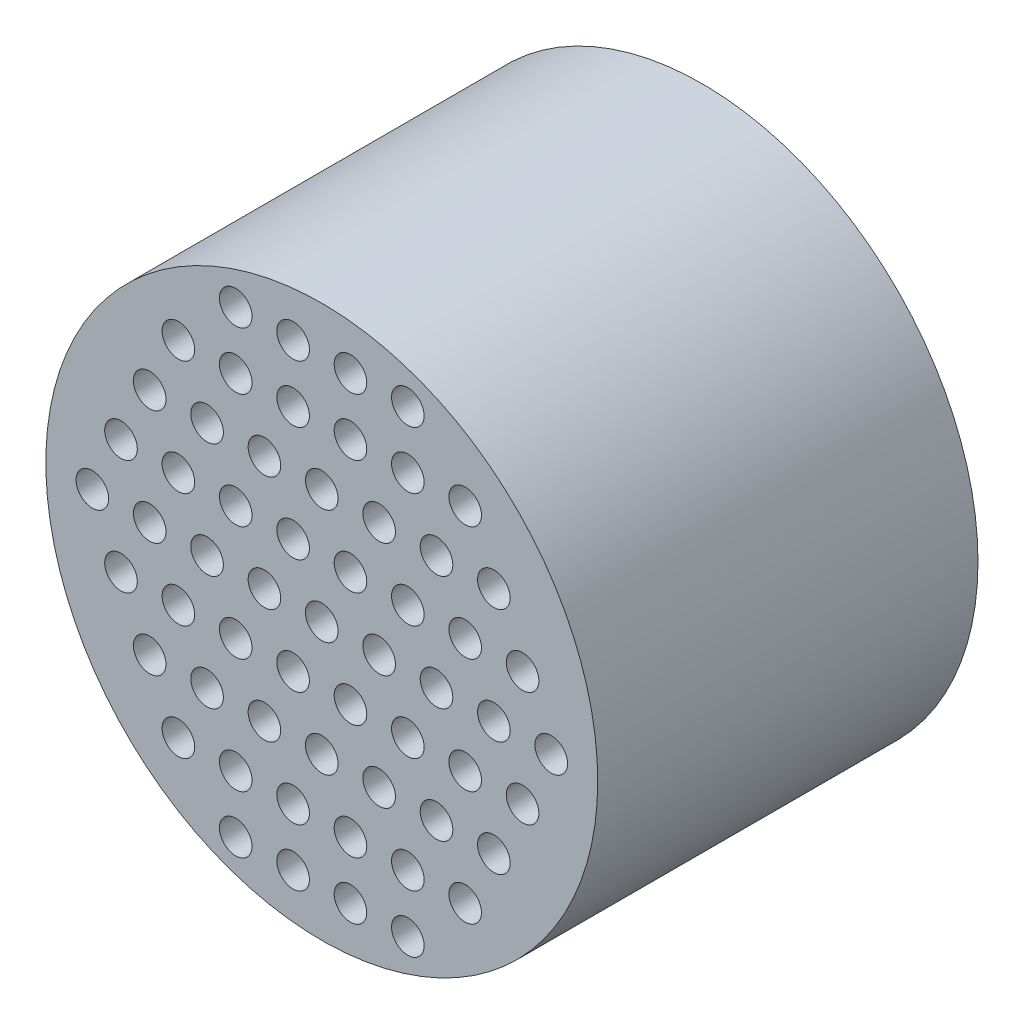
SolidWorks part; units mm, degrees
material "PBT à usage général"
ref_plane "Plan de face" through (0, 0, 0) normal (0, 0, 1) x (1, 0, 0)
ref_plane "Plan de dessus" through (0, 0, 0) normal (0, 1, 0) x (1, 0, 0)
ref_plane "Plan de droite" through (0, 0, 0) normal (1, 0, 0) x (0, 0, -1)
sketch "Esquisse1" plane through (0, 0, 0) normal (0, 0, 1) x (1, 0, 0)
  circle A0 centre (16.6252, 7.1087) radius 25.4
  dimension "D1" = 50.8
extrude "Boss.-Extru.1" add sketch "Esquisse1" along normal blind 25
sketch "Esquisse6" plane through (0, 0, 0) normal (0, 0, -1) x (-1, 0, 0)
  line L0 (-42.0252, 7.1087) -> (8.7748, 7.1087) construction
  circle A0 centre (-16.6252, 7.1087) radius 25.4 construction
  circle A1 centre (-39.5252, 7.1087) radius 1.55
  circle A2 centre (6.2748, 7.1087) radius 1.55
  point P12 (-16.6252, 7.1087)
  dimension "D1" = 3.1
  dimension "D2" = 2.5
  dimension "D3" = 2
extrude "Enlèv. mat.-Extru.4" cut sketch "Esquisse6" against normal blind 6
sketch "Esquisse8" plane through (0, 0, 25) normal (0, 0, 1) x (1, 0, 0)
  line L0 (-8.7748, 7.1087) -> (16.6252, 7.1087) construction
  circle A0 centre (16.6252, 7.1087) radius 25.4 construction
  circle A1 centre (16.6252, 7.1087) radius 25.4
  dimension "D1" = 50.8
extrude "Boss.-Extru.3" add sketch "Esquisse8" along normal blind 10
sketch "Esquisse9" plane through (0, 0, 35) normal (0, 0, 1) x (1, 0, 0)
  line L0 (16.6252, 32.5087) -> (16.6252, 7.1087) construction
  line L1 (11.3452, 7.1087) -> (6.0652, 7.1087) construction
  line L2 (8.7052, 7.1087) -> (8.7052, 12.3887) construction
  circle A0 centre (16.6252, 7.1087) radius 25.4 construction
  circle A1 centre (16.6252, 7.1087) radius 1.5
  circle A60 centre (21.9052, 7.1087) radius 1.5
  circle A62 centre (27.1852, 7.1087) radius 1.5
  circle A63 centre (32.4652, 7.1087) radius 1.5
  circle A66 centre (37.7452, 7.1087) radius 1.5
  circle A67 centre (11.3452, 7.1087) radius 1.5
  circle A68 centre (6.0652, 7.1087) radius 1.5
  circle A69 centre (0.7852, 7.1087) radius 1.5
  circle A70 centre (-4.4948, 7.1087) radius 1.5
  circle A71 centre (0.7852, 17.6687) radius 1.5
  circle A72 centre (6.0652, 17.6687) radius 1.5
  circle A73 centre (11.3452, 17.6687) radius 1.5
  circle A74 centre (16.6252, 17.6687) radius 1.5
  circle A75 centre (21.9052, 17.6687) radius 1.5
  circle A76 centre (27.1852, 17.6687) radius 1.5
  circle A77 centre (32.4652, 17.6687) radius 1.5
  circle A78 centre (8.7052, 12.3887) radius 1.5
  circle A79 centre (13.9852, 12.3887) radius 1.5
  circle A80 centre (19.2652, 12.3887) radius 1.5
  circle A81 centre (24.5452, 12.3887) radius 1.5
  circle A82 centre (29.8252, 12.3887) radius 1.5
  circle A83 centre (35.1052, 12.3887) radius 1.5
  circle A84 centre (3.4252, 12.3887) radius 1.5
  circle A85 centre (-1.8548, 12.3887) radius 1.5
  circle A86 centre (13.9852, 12.3887) radius 1.5 [skipped]
  circle A87 centre (19.2652, 12.3887) radius 1.5 [skipped]
  circle A88 centre (24.5452, 12.3887) radius 1.5 [skipped]
  circle A89 centre (13.9852, 17.6687) radius 1.5 [skipped]
  circle A90 centre (19.2652, 17.6687) radius 1.5 [skipped]
  circle A91 centre (24.5452, 17.6687) radius 1.5 [skipped]
  circle A92 centre (13.9852, 22.9487) radius 1.5
  circle A93 centre (19.2652, 22.9487) radius 1.5
  circle A94 centre (24.5452, 22.9487) radius 1.5
  circle A95 centre (13.9852, 28.2287) radius 1.5
  circle A96 centre (19.2652, 28.2287) radius 1.5
  circle A97 centre (24.5452, 28.2287) radius 1.5
  circle A98 centre (8.7052, 17.6687) radius 1.5 [skipped]
  circle A99 centre (8.7052, 22.9487) radius 1.5
  circle A100 centre (8.7052, 28.2287) radius 1.5
  circle A101 centre (29.8252, 12.3887) radius 1.5 [skipped]
  circle A102 centre (29.8252, 22.9487) radius 1.5
  circle A103 centre (3.4252, 22.9487) radius 1.5
  circle A104 centre (35.1052, 1.8287) radius 1.5
  circle A105 centre (29.8252, 1.8287) radius 1.5
  circle A106 centre (24.5452, 1.8287) radius 1.5
  circle A107 centre (19.2652, 1.8287) radius 1.5
  circle A108 centre (13.9852, 1.8287) radius 1.5
  circle A109 centre (8.7052, 1.8287) radius 1.5
  circle A110 centre (3.4252, 1.8287) radius 1.5
  circle A111 centre (-1.8548, 1.8287) radius 1.5
  circle A112 centre (0.7852, -3.4513) radius 1.5
  circle A113 centre (6.0652, -3.4513) radius 1.5
  circle A114 centre (11.3452, -3.4513) radius 1.5
  circle A115 centre (16.6252, -3.4513) radius 1.5
  circle A116 centre (21.9052, -3.4513) radius 1.5
  circle A117 centre (27.1852, -3.4513) radius 1.5
  circle A118 centre (32.4652, -3.4513) radius 1.5
  circle A119 centre (29.8252, -8.7313) radius 1.5
  circle A120 centre (24.5452, -8.7313) radius 1.5
  circle A121 centre (19.2652, -8.7313) radius 1.5
  circle A122 centre (13.9852, -8.7313) radius 1.5
  circle A123 centre (8.7052, -8.7313) radius 1.5
  circle A124 centre (3.4252, -8.7313) radius 1.5
  circle A125 centre (8.7052, -14.0113) radius 1.5
  circle A126 centre (13.9852, -14.0113) radius 1.5
  circle A127 centre (19.2652, -14.0113) radius 1.5
  circle A128 centre (24.5452, -14.0113) radius 1.5
  point P21 (16.6252, 7.1087)
  point P45 (16.6252, 7.1087)
  point P82 (16.6252, 7.1087)
  point P127 (16.6252, 7.1087)
  point P152 (16.6252, 7.1087)
  dimension "D1" = 3
  dimension "D2" = 5
  dimension "D6" = 3
  dimension "D4" = 2
  dimension "D8" = 6
  dimension "D7" = 5.28
  dimension "D3" = 5
  dimension "D5" = 7
  dimension "D9" = 3
  dimension "D10" = 4
  dimension "D11" = 4
  dimension "D12" = 2
  dimension "D13" = 2
  dimension "D14" = 2
extrude "Enlèv. mat.-Extru.5" cut sketch "Esquisse9" against normal blind 10
sketch "Esquisse10" plane through (0, 0, 35) normal (0, 0, 1) x (1, 0, 0)
  line L0 (0, 7.1087) -> (16.6252, 7.1087) construction
  line L1 (0, -17.9722) -> (0, 17.9722) construction
ref_plane "Plan1" through (16.6252, 0, 0) normal (1, 0, 0) x (0, 0, -1)
sketch "Esquisse12" plane through (16.6252, 0, 0) normal (1, 0, 0) x (0, 0, -1)
  line L0 (-35, 32.5087) -> (-35, 7.1087) construction
  line L1 (-35, 32.5087) -> (-35, -18.2913) construction
  line L2 (-35, 7.1087) -> (0, 7.1087) construction
  line L3 (0, 55) -> (0, -55) construction
  line L4 (0, 7.1087) -> (0, 27.1087)
  line L5 (0, 27.1087) -> (-25, 30.1087)
  line L6 (-25, 30.1087) -> (-25, 7.1087)
  line L7 (-25, 7.1087) -> (0, 7.1087)
  dimension "D1" = 23
  dimension "D2" = 20
  dimension "D3" = 10
revolve "Enlèvement de matière-Révolution1" cut sketch "Esquisse12" angle 360 about L7
